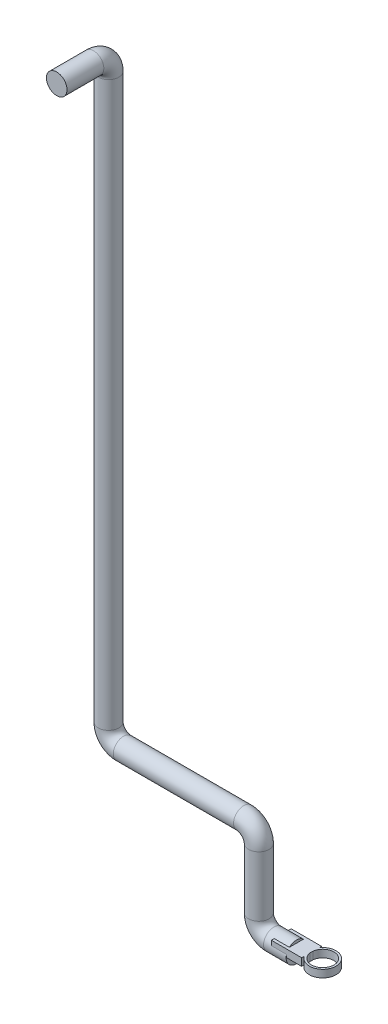
SolidWorks part; units mm, degrees
ref_plane "Alzado" through (0, 0, 0) normal (0, 0, 1) x (1, 0, 0)
ref_plane "Planta" through (0, 0, 0) normal (0, 1, 0) x (1, 0, 0)
ref_plane "Vista lateral" through (0, 0, 0) normal (1, 0, 0) x (0, 0, -1)
sketch3d "Croquis3D1"
  line L0 (0, 0, 0) -> (-30, 0, 0)
  line L1 (-50, 20, 0) -> (-50, 100, 0)
  line L2 (-70, 120, 0) -> (-230, 120, 0)
  line L3 (-250, 140, 0) -> (-250, 890, 0)
  line L4 (-250, 910, 20) -> (-250, 910, 80)
  line L5 (-250, 930, 100) -> (-250, 940, 100)
  line L6 (-250, 960, 120) -> (-250, 960, 150)
  arc A0 (-250, 940, 100) -> (-250, 960, 120) centre (-250, 940, 120) ccw
  arc A1 (-250, 910, 80) -> (-250, 930, 100) centre (-250, 930, 80) ccw
  arc A2 (-250, 890, 0) -> (-250, 910, 20) centre (-250, 890, 20) ccw
  arc A3 (-230, 120, 0) -> (-250, 140, 0) centre (-230, 140, 0) ccw
  arc A4 (-50, 100, 0) -> (-70, 120, 0) centre (-70, 100, 0) ccw
  arc A5 (-30, 0, 0) -> (-50, 20, 0) centre (-30, 20, 0) ccw
  point P11 (-250, 960, 100)
  point P12 (-230, 940, 120)
  point P15 (-250, 910, 100)
  point P16 (-270, 930, 80)
  point P19 (-250, 910, 0)
  point P20 (-230, 890, 20)
  point P23 (-250, 120, 0)
  point P24 (-230, 140, -20)
  point P27 (-50, 120, 0)
  point P28 (-70, 100, 20)
  point P31 (-50, 0, 0)
  point P32 (-30, 20, -20)
  dimension "D8" = 20
  dimension "D1" = 50
  dimension "D2" = 120
  dimension "D3" = 200
  dimension "D4" = 790
  dimension "D5" = 100
  dimension "D6" = 50
  dimension "D7" = 50
sketch "Croquis1" plane through (0, 0, 0) normal (1, 0, 0) x (0, 0, -1)
  circle A0 centre (0, 0) radius 13.7
  dimension "D1" = 27.4
sweep "Barrer1" add profiles "Croquis1" path "Croquis3D1"
ref_plane "Plano1" through (0, 0, 0) normal (1, 0, 0) x (0, 0, -1)
sketch "Croquis2" plane through (0, 0, 150) normal (0, 0, 1) x (1, 0, 0)
  line L1 (-302.4054, 855.9914) -> (-197.5946, 855.9914)
  line L2 (-302.4054, 855.9914) -> (-302.4054, 1064.0086)
  line L3 (-302.4054, 1064.0086) -> (-197.5946, 1064.0086)
  line L4 (-197.5946, 855.9914) -> (-197.5946, 1064.0086)
  line L5 (-302.4054, 855.9914) -> (-197.5946, 1064.0086) construction
  line L6 (-302.4054, 1064.0086) -> (-197.5946, 855.9914) construction
  point P0 (-250, 960)
extrude "Cortar-Extruir2" cut sketch "Croquis2" against normal blind 81
sketch "Croquis3" plane through (0, 0, 0) normal (0, 1, 0) x (1, 0, 0)
  line L0 (0, 0) -> (35, 0) construction
  circle A0 centre (35, 0) radius 15
  circle A1 centre (35, 0) radius 17.7625
  dimension "D1" = 30
  dimension "D2" = 35
extrude "Saliente-Extruir1" add sketch "Croquis3" along normal blind 10 separate body
sketch "Croquis4" plane through (0, 0, 0) normal (0, 1, 0) x (1, 0, 0)
  line L1 (-20.1475, 13.1948) -> (20.1475, 13.1948)
  line L2 (-20.1475, 13.1948) -> (-20.1475, -13.1948)
  line L3 (-20.1475, -13.1948) -> (20.1475, -13.1948)
  line L4 (20.1475, 13.1948) -> (20.1475, -13.1948)
  line L5 (-20.1475, 13.1948) -> (20.1475, -13.1948) construction
  line L6 (-20.1475, -13.1948) -> (20.1475, 13.1948) construction
  point P0 (0, 0)
extrude "Saliente-Extruir2" add sketch "Croquis4" along normal blind 10
